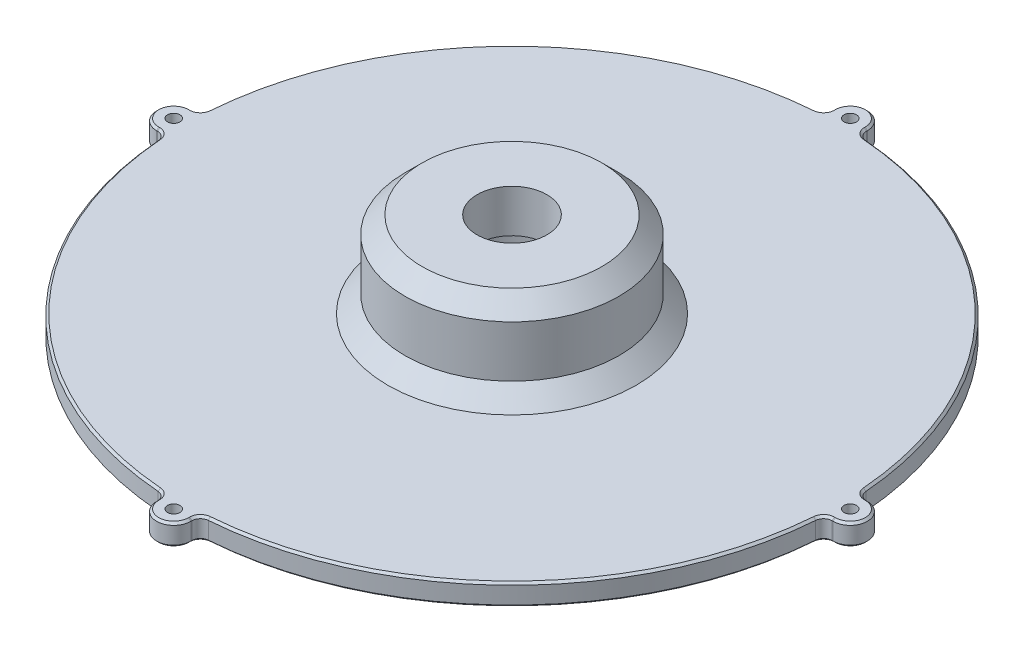
SolidWorks part; units mm, degrees
ref_plane "Płaszczyzna przednia" through (0, 0, 0) normal (0, 0, 1) x (1, 0, 0)
ref_plane "Płaszczyzna górna" through (0, 0, 0) normal (0, 1, 0) x (1, 0, 0)
ref_plane "Płaszczyzna prawa" through (0, 0, 0) normal (1, 0, 0) x (0, 0, -1)
sketch "Szkic2" plane through (0, 0, 0) normal (0, 0, 1) x (1, 0, 0)
  line L0 (15, 5) -> (15, 0)
  line L1 (15, 0) -> (77, 0)
  line L2 (77, 0) -> (77, 5)
  line L5 (77, 5) -> (15, 5)
  line L6 (0, 0) -> (0, 12.2819) construction
  line L7 (15, 5) -> (15, 15)
  line L8 (15, 15) -> (8.15, 15)
  line L9 (8.15, 15) -> (8.15, 25)
  line L10 (8.15, 25) -> (25, 25)
  line L11 (25, 25) -> (25, 5)
  dimension "D1" = 77
  dimension "D2" = 16.3
  dimension "D3" = 10
  dimension "D4" = 5
  dimension "D5" = 15
  dimension "D6" = 10
  dimension "D7" = 25
revolve "Obrót1" add sketch "Szkic2" angle 360 about L6
sketch "Szkic3" plane through (0, 5, 0) normal (0, 1, 0) x (1, 0, 0)
  line L0 (0, 76.5) -> (0, 79) construction
  line L1 (-4, 76.5) -> (-4, 79)
  line L2 (4, 76.5) -> (4, 79)
  line L3 (76.5, 0) -> (79, 0) construction
  line L4 (76.5, 4) -> (79, 4)
  line L5 (76.5, -4) -> (79, -4)
  line L6 (0, -76.5) -> (0, -79) construction
  line L7 (4, -76.5) -> (4, -79)
  line L8 (-4, -76.5) -> (-4, -79)
  line L9 (-76.5, 0) -> (-79, 0) construction
  line L10 (-76.5, -4) -> (-79, -4)
  line L11 (-76.5, 4) -> (-79, 4)
  arc A1 (-4, 76.5) -> (4, 76.5) centre (0, 76.5) ccw
  arc A2 (4, 79) -> (-4, 79) centre (0, 79) ccw
  circle A3 centre (0, 79) radius 1.45
  circle A4 centre (79, 0) radius 1.45
  arc A5 (76.5, 4) -> (76.5, -4) centre (76.5, 0) ccw
  arc A6 (79, -4) -> (79, 4) centre (79, 0) ccw
  circle A7 centre (0, -79) radius 1.45
  arc A8 (4, -76.5) -> (-4, -76.5) centre (0, -76.5) ccw
  arc A9 (-4, -79) -> (4, -79) centre (0, -79) ccw
  circle A10 centre (-79, 0) radius 1.45
  arc A11 (-76.5, -4) -> (-76.5, 4) centre (-76.5, 0) ccw
  arc A12 (-79, 4) -> (-79, -4) centre (-79, 0) ccw
  point P6 (0, 77.75)
  point P18 (77.75, 0)
  point P27 (0, -77.75)
  point P36 (-77.75, 0)
  point P43 (0, 0)
  dimension "D1" = 2.9
  dimension "D2" = 4
  dimension "D3" = 2.5
  dimension "D5" = 79
  dimension "D4" = 4
extrude "Dodanie-wyciągnięcie1" add sketch "Szkic3" against normal blind 5
sketch "Szkic4" plane through (0, 5, 0) normal (0, 1, 0) x (1, 0, 0)
  line L1 (-12.5, 12.5) -> (12.5, 12.5) construction
  line L2 (-12.5, 12.5) -> (-12.5, -12.5) construction
  line L3 (-12.5, -12.5) -> (12.5, -12.5) construction
  line L4 (12.5, 12.5) -> (12.5, -12.5) construction
  line L5 (-12.5, 12.5) -> (12.5, -12.5) construction
  line L6 (-12.5, -12.5) -> (12.5, 12.5) construction
  circle A0 centre (12.5, 12.5) radius 3.1
  circle A1 centre (12.5, -12.5) radius 3.1
  circle A2 centre (-12.5, -12.5) radius 3.1
  circle A3 centre (-12.5, 12.5) radius 3.1
  point P0 (0, 0)
  dimension "D2" = 6.2
  dimension "D1" = 25
chamfer "Sfazowanie1" distance 4 angle 45 2 edges at (0, 5, -25) (0, 25, -25)
fillet "Zaokrąglenie1" radius 2 8 edges at (76.896, 2.5, 4) (76.896, 2.5, -4) (4, 2.5, 76.896) (-4, 2.5, 76.896) (-76.896, 2.5, 4) (-76.896, 2.5, -4) (4, 2.5, -76.896) (-4, 2.5, -76.896)
chamfer "Sfazowanie2" distance 0.5 angle 45 53 edges at (4, 5, -78.8859) (4, 0, -78.8859) (-4, 5, -78.8859) (-4, 0, -78.8859) (77.4124, 5, 4.5331) (77.4124, 0, 4.5331) (77.4124, 5, -4.5331) (77.4124, 0, -4.5331) (4.5331, 5, 77.4124) (4.5331, 0, 77.4124) (-4.5331, 5, 77.4124) (-4.5331, 0, 77.4124) (-77.4124, 5, 4.5331) (-77.4124, 0, 4.5331) (-77.4124, 5, -4.5331) (-77.4124, 0, -4.5331) (4.5331, 5, -77.4124) (4.5331, 0, -77.4124) (-4.5331, 5, -77.4124) (-4.5331, 0, -77.4124) (-83, 0, 0) (-79, 0, 1.45) (-83, 5, 0) (0, 0, 83) (0, 0, 80.45) (0, 5, 83) (83, 0, 0) (79, 0, 1.45) (83, 5, 0) (0, 0, -83) (0, 0, -77.55) (0, 5, -83) (0, 0, -15) (54.4472, 5, 54.4472) (54.4472, 0, 54.4472) (78.8859, 5, 4) (78.8859, 0, 4) (78.8859, 5, -4) (78.8859, 0, -4) (54.4472, 5, -54.4472) (54.4472, 0, -54.4472) (4, 5, 78.8859) (4, 0, 78.8859) (-54.4472, 5, 54.4472) (-54.4472, 0, 54.4472) (-4, 5, 78.8859) (-4, 0, 78.8859) (-78.8859, 5, 4) (-78.8859, 0, 4) (-54.4472, 5, -54.4472) (-54.4472, 0, -54.4472) (-78.8859, 5, -4) (-78.8859, 0, -4)
